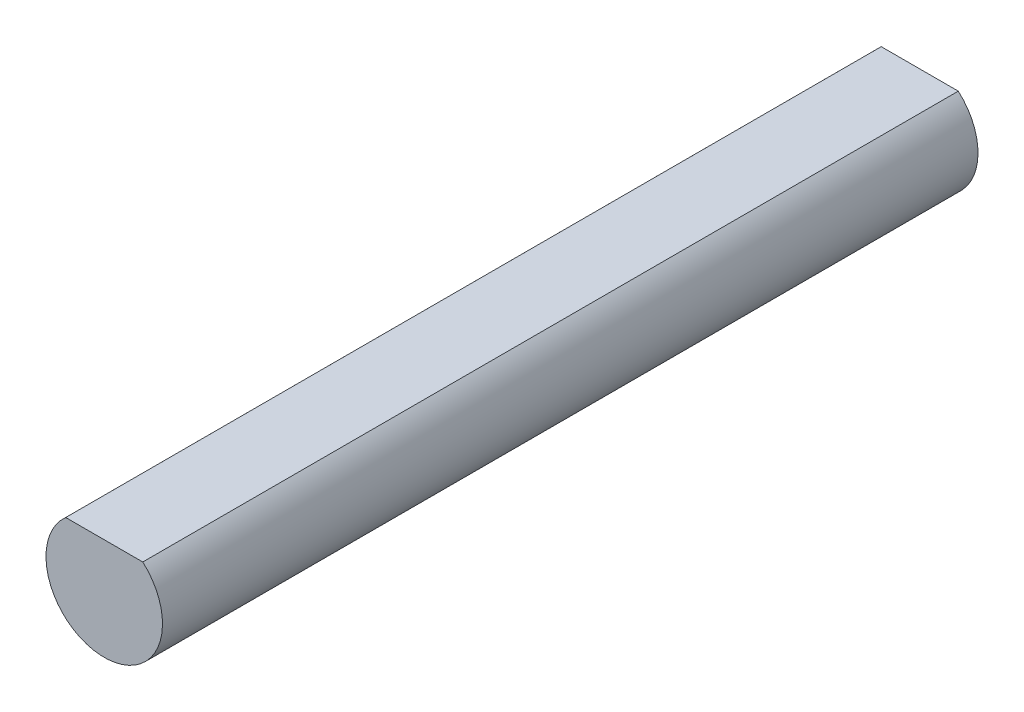
SolidWorks part; units mm, degrees
material "Stainless Steel (ferritic)"
ref_plane "Front Plane" through (0, 0, 0) normal (0, 0, 1) x (1, 0, 0)
ref_plane "Top Plane" through (0, 0, 0) normal (0, 1, 0) x (1, 0, 0)
ref_plane "Right Plane" through (0, 0, 0) normal (1, 0, 0) x (0, 0, -1)
sketch "Sketch1" plane through (0, 0, 0) normal (0, 0, 1) x (1, 0, 0)
  line L0 (-1.3229, 1.5) -> (1.3229, 1.5)
  arc A0 (-1.3229, 1.5) -> (1.3229, 1.5) centre (0, 0) ccw
  dimension "D1" = 4
  dimension "D2" = 3.5
extrude "Boss-Extrude1" add sketch "Sketch1" along normal blind 28
